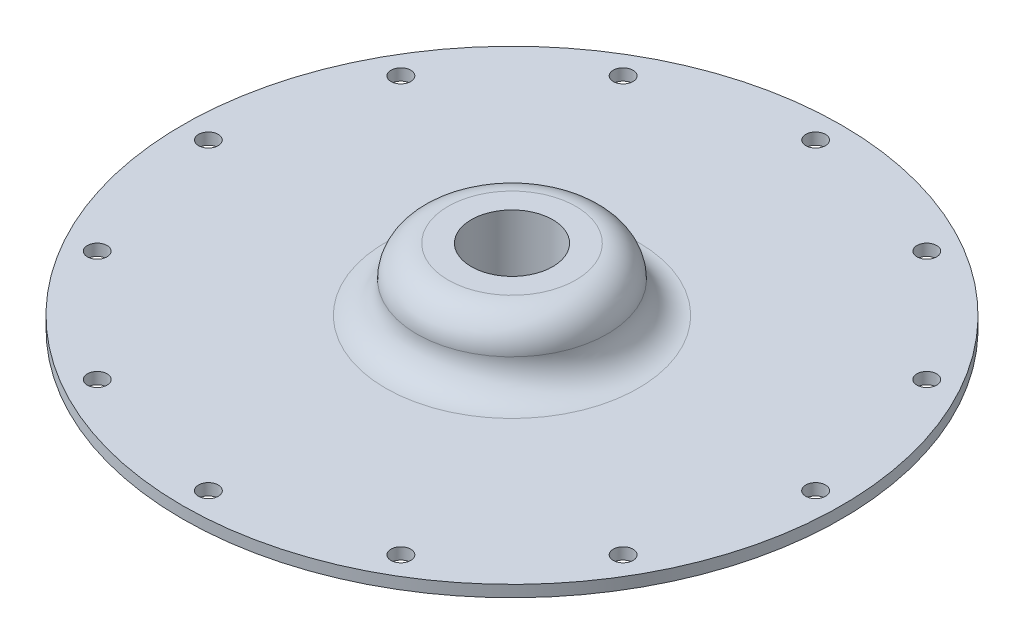
SolidWorks part; units mm, degrees
material "6063-T6"
ref_plane "Front Plane" through (0, 0, 0) normal (0, 0, 1) x (1, 0, 0)
ref_plane "Top Plane" through (0, 0, 0) normal (0, 1, 0) x (1, 0, 0)
ref_plane "Right Plane" through (0, 0, 0) normal (1, 0, 0) x (0, 0, -1)
ref_axis "Axis1" through (0, 55, 0) along (0, -1, 0)
sketch "Sketch1" plane through (0, 0, 0) normal (0, 0, 1) x (1, 0, 0)
  line L0 (-45.212, 0) -> (-5.588, 0)
  line L1 (0, 55) -> (0, -55) construction
  line L2 (-45.212, 0) -> (-45.212, 1.5875)
  line L3 (-5.588, 10.16) -> (-8.763, 10.16)
  line L5 (-5.588, 10.16) -> (-5.588, 0)
  line L6 (-5.588, 0) -> (0, 0) construction
  line L7 (-45.212, 0) -> (-45.212, 1.5875) construction
  line L8 (-5.588, 1.5875) -> (-5.588, 0) construction
  line L9 (-45.212, 1.5875) -> (-17.3355, 1.5875)
  arc A0 (-17.3355, 1.5875) -> (-13.0493, 5.8738) centre (-17.3355, 5.8738) ccw
  arc A1 (-13.0493, 5.8738) -> (-8.763, 10.16) centre (-8.763, 5.8738) cw
  dimension "D1" = 10.16
  dimension "D2" = 3.175
  dimension "D3" = 1.5875
revolve "Revolve1" add sketch "Sketch1" angle 360 about axis through (0, 55, 0) along (0, -1, 0)
ref_plane "Hole Location Plane" through (0, 3.175, 0) normal (0, 1, 0) x (1, 0, 0)
sketch "Hole Location" plane through (0, 3.175, 0) normal (0, 1, 0) x (1, 0, 0)
  line L0 (0, 0) -> (-41.656, 0) construction
  circle A0 centre (0, 0) radius 41.656 construction
  dimension "D1" = 83.312
hole_wizard "#36 (0.1065) Diameter Hole1" positions "Sketch2" profile "Sketch3" hole size "#36" standard "ANSI Inch" end condition through all
sketch "Sketch2" plane through (0, 0, 0) normal (0, -1, 0) x (-1, 0, 0)
  line L0 (0, 0) -> (41.656, 0) construction
  point P0 (41.656, 0)
sketch "Sketch3" plane through (-41.656, 0, 0) normal (1, 0, 0) x (0, 0, -1)
  line L0 (0, 0) -> (0, 10.16)
  line L1 (0, 10.16) -> (1.3525, 10.16)
  line L2 (1.3525, 10.16) -> (1.3525, 0)
  line L5 (1.3525, 0) -> (0, 0)
  line L11 (0, -6.35) -> (0, 107.95) construction
  dimension "Thru Hole Dia." = 2.7051
  dimension "Thru Hole Depth" = 10.16
pattern_circular "CirPattern1" count 12 over 360 about axis through (0, 0, 0) along (0, 1, 0) of "#36 (0.1065) Diameter Hole1"
equation "\"D1@Hole Location\"=\"TANK DIAMETER@Cryo Tank.Assembly\"+\"GASKET SEAT THICKNESS@Cryo Tank.Assembly\""
